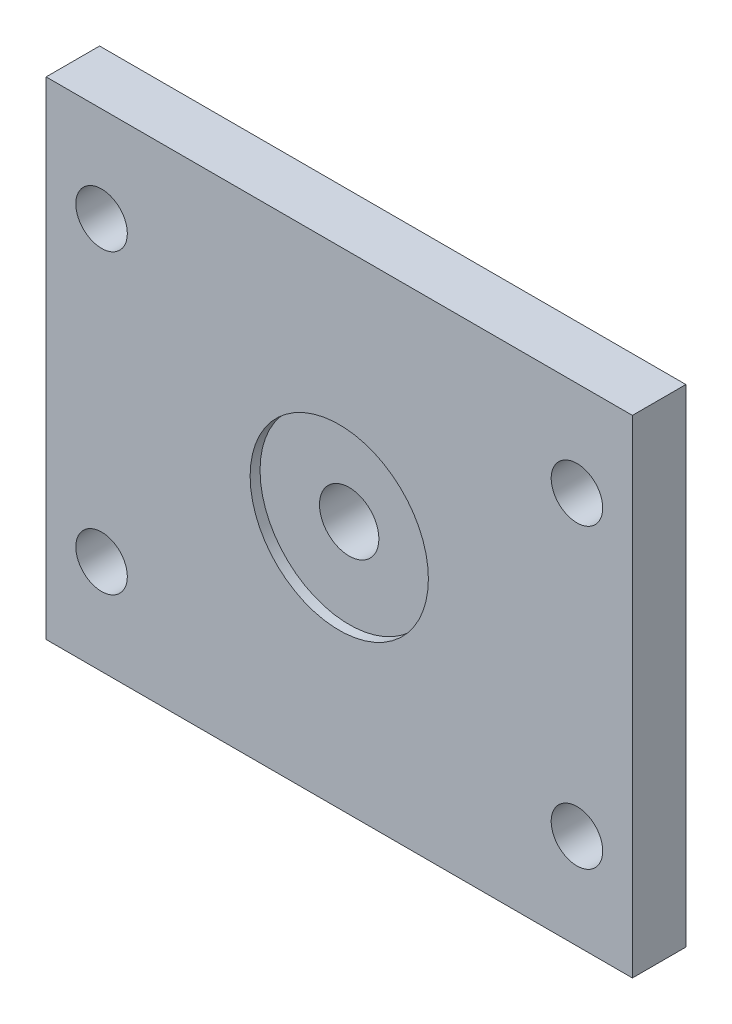
SolidWorks part; units mm, degrees
ref_plane "Front Plane" through (0, 0, 0) normal (0, 0, 1) x (1, 0, 0)
ref_plane "Top Plane" through (0, 0, 0) normal (0, 1, 0) x (1, 0, 0)
ref_plane "Right Plane" through (0, 0, 0) normal (1, 0, 0) x (0, 0, -1)
sketch "Sketch1" plane through (0, 0, 0) normal (0, 0, 1) x (1, 0, 0)
  line L1 (148, -123) -> (-148, -123)
  line L2 (148, -123) -> (148, 123)
  line L3 (148, 123) -> (-148, 123)
  line L4 (-148, -123) -> (-148, 123)
  line L5 (148, -123) -> (-148, 123) construction
  line L6 (148, 123) -> (-148, -123) construction
  circle A0 centre (-120, 75) radius 13 construction
  circle A1 centre (120, 75) radius 13 construction
  circle A2 centre (120, -75) radius 13 construction
  circle A3 centre (-120, -75) radius 13 construction
  circle A4 centre (-120, 75) radius 13
  circle A5 centre (120, 75) radius 13
  circle A6 centre (120, -75) radius 13
  circle A7 centre (-120, -75) radius 13
  circle A8 centre (0, 0) radius 15
  point P0 (0, 0)
  dimension "D3" = 30
  dimension "D1" = 296
  dimension "D2" = 246
extrude "Extrude1" add sketch "Sketch1" along normal blind 27
sketch "Sketch2" plane through (0, 0, 27) normal (0, 0, 1) x (1, 0, 0)
  circle A0 centre (0, 0) radius 45
  dimension "D1" = 90
extrude "Extrude2" cut sketch "Sketch2" against normal blind 5
